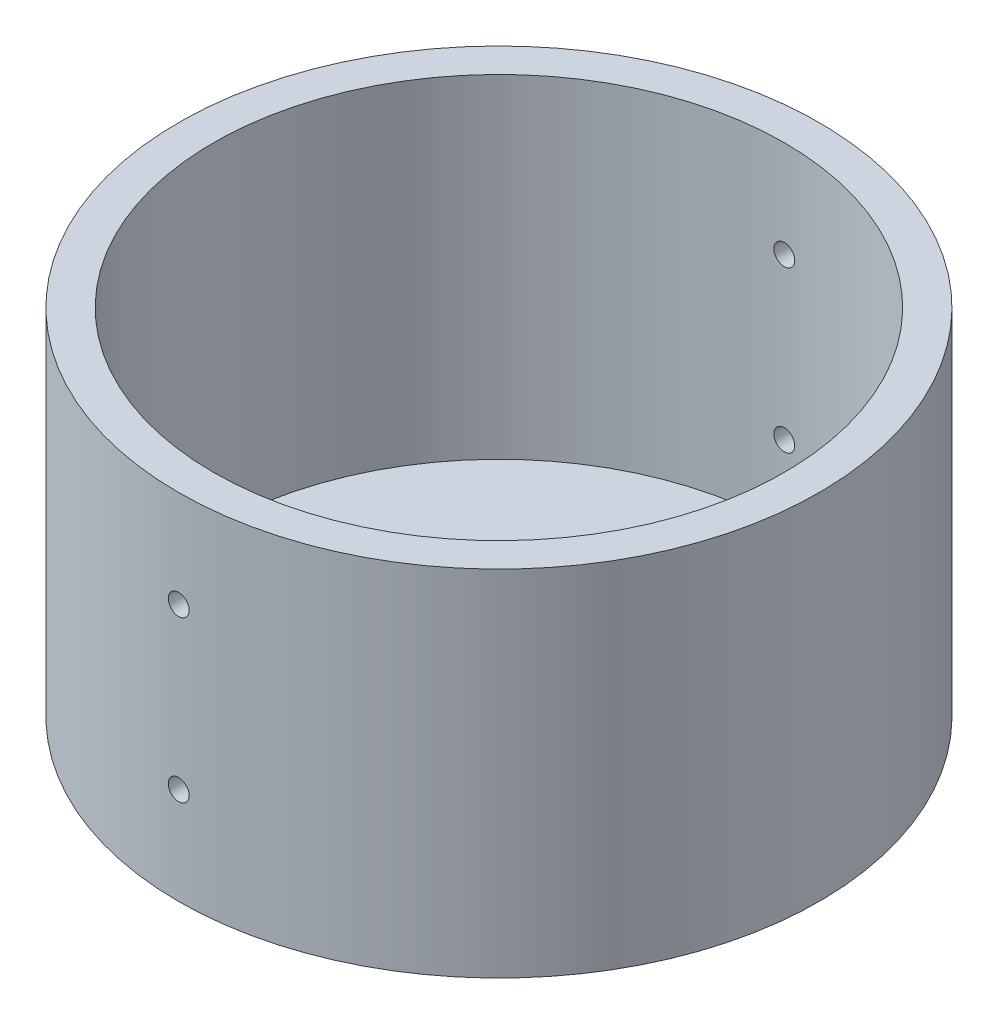
SolidWorks part; units mm, degrees
ref_plane "Front Plane" through (0, 0, 0) normal (0, 0, 1) x (1, 0, 0)
ref_plane "Top Plane" through (0, 0, 0) normal (0, 1, 0) x (1, 0, 0)
ref_plane "Right Plane" through (0, 0, 0) normal (1, 0, 0) x (0, 0, -1)
sketch "Sketch1" plane through (0, 0, 0) normal (0, 1, 0) x (1, 0, 0)
  circle A0 centre (0, 0) radius 45.95
  dimension "D1" = 91.9
extrude "Boss-Extrude1" add sketch "Sketch1" along normal blind 3
sketch "Sketch2" plane through (0, 3, 0) normal (0, 1, 0) x (1, 0, 0)
  circle A0 centre (0, 0) radius 45.95
  circle A1 centre (0, 0) radius 40.95
  dimension "D1" = 5
extrude "Boss-Extrude2" add sketch "Sketch2" along normal blind 22.4
sketch "Sketch3" plane through (0, 0, 0) normal (0, -1, 0) x (1, 0, 0)
  circle A0 centre (0, 0) radius 45.95
  circle A1 centre (0, 0) radius 42.95
  dimension "D1" = 3
sketch "Sketch6" plane through (0, 0, 0) normal (0, -1, 0) x (-1, 0, 0)
  line L0 (0, 0) -> (9.5, 0) construction
  circle A0 centre (0, 0) radius 9.5
  dimension "D1" = 19
hole_wizard "#4-40 Tapped Hole3" positions "Sketch10" profile "Sketch9" tap size "#4-40" standard "ANSI Inch"
sketch "Sketch10" plane through (0, 0, 0) normal (0, -1, 0) x (-1, 0, 0)
  point P0 (9.5, 0)
  point P13 (4.75, -8.2272)
  point P14 (-4.75, -8.2272)
  point P15 (-9.5, 0)
  point P16 (-4.75, 8.2272)
  point P17 (4.75, 8.2272)
  dimension "D1" = 6
sketch "Sketch9" plane through (-9.5, 0, 0) normal (1, 0, 0) x (0, 0, -1)
  line L0 (0, 0) -> (0, 8.2792)
  line L1 (0, 8.2792) -> (1.1303, 7.6)
  line L2 (1.1303, 7.6) -> (1.1303, 0)
  line L5 (1.1303, 0) -> (0, 0)
  line L10 (0, 8.2792) -> (-1.1303, 7.6) construction
  line L11 (0, -6.35) -> (0, 107.95) construction
  dimension "Tap Drill Dia." = 2.2606
  dimension "Tap Drill Depth" = 7.6
  dimension "Drill Angle" = 118
cosmetic thread "Hole Thread9"
cosmetic thread "Hole Thread10"
cosmetic thread "Hole Thread11"
cosmetic thread "Hole Thread12"
cosmetic thread "Hole Thread13"
cosmetic thread "Hole Thread14"
sketch "Sketch11" plane through (0, 0, 0) normal (0, 0, 1) x (1, 0, 0)
  line L0 (0, 0) -> (0, 13.9) construction
  line L1 (-4.444, 0) -> (5.3042, 0) construction
  line L2 (-9.5, 0) -> (9.5, 0) construction
  line L4 (45.95, 25.4) -> (-45.95, 25.4) construction
  circle A0 centre (0, 13.9) radius 1.5
  circle A1 centre (0, -13.9) radius 1.5
  dimension "D2" = 3
  dimension "D3" = 11.5
  dimension "D1" = 13.9
extrude "Cut-Extrude1" cut sketch "Sketch11" against normal through all and the other way through all
sketch "Sketch12" plane through (0, 25.4, 0) normal (0, 1, 0) x (1, 0, 0)
  circle A0 centre (0, 0) radius 45.95
  circle A1 centre (0, 0) radius 40.95
extrude "Boss-Extrude3" add sketch "Sketch12" along normal blind 25.4
sketch "Sketch14" plane through (0, 0, 0) normal (0, 0, 1) x (1, 0, 0)
  line L0 (0, 13.9) -> (0, 36.9) construction
  circle A0 centre (0, 36.9) radius 1.5
  dimension "D2" = 3
  dimension "D1" = 23
extrude "Cut-Extrude2" cut sketch "Sketch14" against normal through all and the other way through all
sketch "Sketch15" plane through (0, 3, 0) normal (0, 1, 0) x (1, 0, 0)
  circle A0 centre (0, 0) radius 3
  dimension "D1" = 6
extrude "Cut-Extrude3" cut sketch "Sketch15" against normal blind 10
